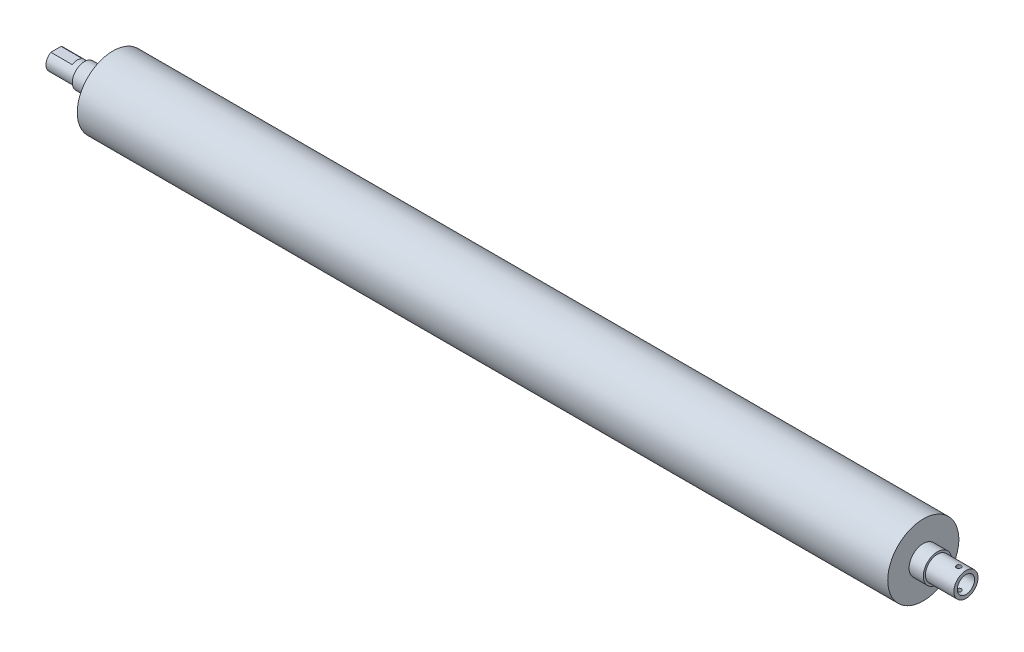
SolidWorks part; units mm, degrees
ref_plane "前视基准面" through (0, 0, 0) normal (0, 0, 1) x (1, 0, 0)
ref_plane "上视基准面" through (0, 0, 0) normal (0, 1, 0) x (1, 0, 0)
ref_plane "右视基准面" through (0, 0, 0) normal (1, 0, 0) x (0, 0, -1)
sketch "草图2" plane through (0, 0, 0) normal (0, 0, 1) x (1, 0, 0)
  line L0 (-62.7059, 0) -> (66, 0) construction
  line L3 (554.4406, 10) -> (544.4406, 10)
  line L4 (544.4406, 10) -> (544.4406, 25)
  line L5 (544.4406, 25) -> (-25.5594, 25)
  line L6 (-25.5594, 25) -> (-25.5594, 10)
  line L7 (-25.5594, 10) -> (-35.5594, 10)
  line L8 (-35.5594, 10) -> (-35.5594, 8.5)
  line L9 (-35.5594, 8.5) -> (-45.5594, 8.5)
  line L10 (-45.5594, 8.5) -> (-45.5594, 7)
  line L11 (554.4406, 10) -> (554.4406, 8.5)
  line L12 (554.4406, 8.5) -> (574.4406, 8.5)
  line L13 (574.4406, 8.5) -> (574.4406, 0)
  line L14 (-51.631, 0) -> (574.4406, 0)
  line L18 (-45.5594, 7) -> (-65.5594, 7)
  line L19 (-65.5594, 7) -> (-65.5594, 0)
  line L20 (-65.5594, 0) -> (-51.631, 0)
  dimension "D1" = 8.5
  dimension "D2" = 10
  dimension "D3" = 10
  dimension "D4" = 570
  dimension "D5" = 25
  dimension "D6" = 10
  dimension "D7" = 20
  dimension "D8" = 20
  dimension "D9" = 7
revolve "旋转1" add sketch "草图2" angle 360 about L0
sketch "草图4" plane through (-65.5594, 0, 0) normal (-1, 0, 0) x (0, 0, 1)
  line L0 (-8, 6) -> (8, 6)
  arc A0 (8, 6) -> (-8, 6) centre (0, 0) ccw
  dimension "D1" = 6
  dimension "D2" = 10
extrude "切除-拉伸2" cut sketch "草图4" against normal blind 15
sketch "草图5" plane through (574.4406, 0, 0) normal (1, 0, 0) x (0, 0, -1)
  circle A0 centre (0, 0) radius 2.55
  dimension "D1" = 5.1
hole_wizard "大小mm Clearance 暗销孔1" positions "草图6" profile "草图7" hole size "Ø12.0" standard "GB"
sketch "草图6" plane through (574.4406, 0, 0) normal (1, 0, 0) x (0, 0, -1)
  point P0 (0, 0)
sketch "草图7" plane through (574.4406, 0, 0) normal (0, 1, 0) x (0, 0, -1)
  line L0 (0, 0) -> (0, 15.6352)
  line L1 (0, 15.6352) -> (6.05, 12)
  line L2 (6.05, 12) -> (6.05, 0)
  line L5 (6.05, 0) -> (0, 0)
  line L10 (0, 15.6352) -> (-6.05, 12) construction
  line L11 (0, -6.35) -> (0, 107.95) construction
  dimension "孔直径" = 12.1
  dimension "孔深度" = 12
  dimension "导头角度" = 118
ref_plane "基准面1" through (0, 8.5, 0) normal (0, 1, 0) x (1, 0, 0)
sketch "草图8" plane through (0, 8.5, 0) normal (0, 1, 0) x (1, 0, 0)
  line L0 (578.9233, 0) -> (517.963, 0) construction
  line L1 (554.4406, -10) -> (554.4406, 10) construction
  circle A0 centre (569.4406, 0) radius 2
  dimension "D1" = 4
  dimension "D2" = 15
hole_wizard "M4 螺纹孔3" positions "草图9" profile "草图10" tap size "M4" standard "GB"
sketch "草图9" plane through (0, 8.5, 0) normal (0, 1, 0) x (1, 0, 0)
  point P0 (569.4406, 0)
sketch "草图10" plane through (569.4406, 8.5, 0) normal (1, 0, 0) x (0, 0, 1)
  line L0 (0, 0) -> (0, 25.9914)
  line L1 (0, 25.9914) -> (1.65, 25)
  line L2 (1.65, 25) -> (1.65, 0)
  line L5 (1.65, 0) -> (0, 0)
  line L10 (0, 25.9914) -> (-1.65, 25) construction
  line L11 (0, -6.35) -> (0, 107.95) construction
  dimension "螺纹孔钻头直径" = 3.3
  dimension "螺纹孔钻头深度" = 25
  dimension "导头角度" = 118
cosmetic thread "孔螺蚊线1" parameters "D1"=8, "D2"=4
